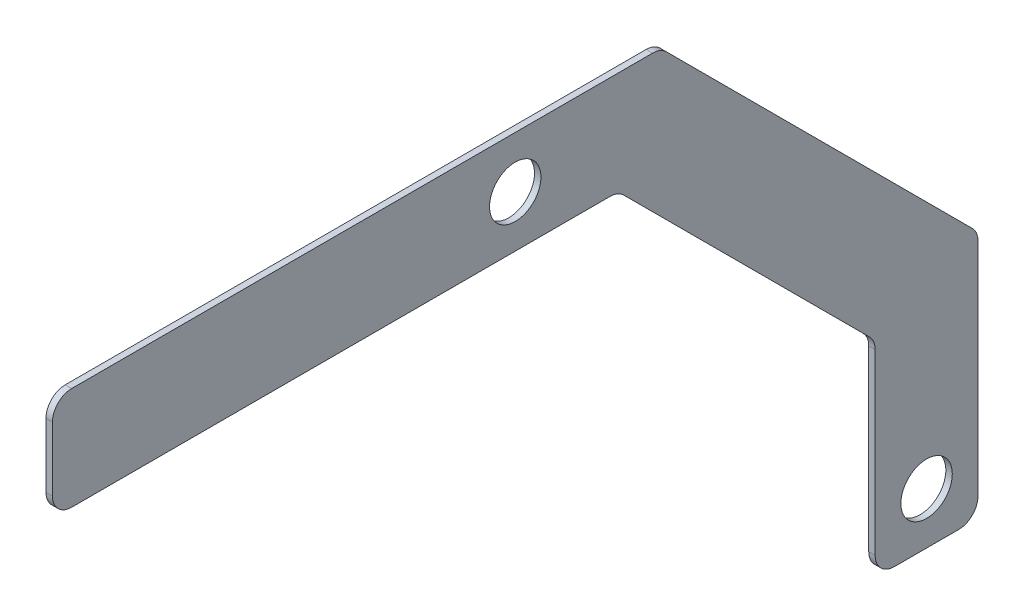
SolidWorks part; units mm, degrees
material "6063-O"
ref_plane "Front" through (0, 0, 0) normal (0, 0, 1) x (1, 0, 0)
ref_plane "Top" through (0, 0, 0) normal (0, 1, 0) x (1, 0, 0)
ref_plane "Right" through (0, 0, 0) normal (1, 0, 0) x (0, 0, -1)
sketch "Sketch1" plane through (0, 0, 0) normal (1, 0, 0) x (0, 0, -1)
  line L0 (0, 25.4) -> (0, -25.4) construction
  line L1 (-228.6, 25.4) -> (228.6, 25.4)
  line L2 (-228.6, 25.4) -> (-228.6, -254)
  line L3 (-177.8, -25.4) -> (177.8, -25.4)
  line L4 (228.6, 25.4) -> (228.6, -254)
  line L7 (228.6, -254) -> (177.8, -254)
  line L8 (177.8, -25.4) -> (177.8, -254)
  line L11 (-228.6, -254) -> (-177.8, -254)
  line L12 (-177.8, -25.4) -> (-177.8, -254)
  circle A0 centre (0, 0) radius 12.7
  point P12 (0, 0)
  dimension "D5" = 25.4
  dimension "D1" = 50.8
  dimension "D2" = 50.8
  dimension "D3" = 457.2
  dimension "D4" = 228.6
extrude "Boss-Extrude1" add sketch "Sketch1" along normal blind 3.175
sketch "Sketch3" plane through (3.175, 0, 0) normal (1, 0, 0) x (0, 0, -1)
  line L0 (-279.2989, -228.6) -> (49720.7011, -228.6) construction
  line L1 (-228.6, -254) -> (-177.8, -254) construction
  line L2 (-203.2, -254) -> (-203.2, 25.4) construction
  line L3 (228.6, 25.4) -> (-228.6, 25.4) construction
  line L4 (203.2, -254) -> (203.2, 25.4) construction
  line L5 (177.8, -254) -> (228.6, -254) construction
  circle A0 centre (-203.2, -228.6) radius 12.7
  circle A1 centre (203.2, -228.6) radius 12.7
  point P12 (-203.2, -228.6)
  point P13 (203.2, -228.6)
  dimension "D2" = 25.4
  dimension "D1" = 25.4
extrude "Cut-Extrude1" cut sketch "Sketch3" against normal through all
sketch "Sketch4" plane through (3.175, 0, 0) normal (1, 0, 0) x (0, 0, -1)
  line L1 (-177.8, -25.4) -> (-228.6, -25.4)
  line L2 (-177.8, -25.4) -> (-177.8, -254)
  line L3 (-177.8, -254) -> (-228.6, -254)
  line L4 (-228.6, -25.4) -> (-228.6, -254)
extrude "Cut-Extrude2" cut sketch "Sketch4" against normal through all
sketch "Sketch5" plane through (3.175, 0, 0) normal (1, 0, 0) x (0, 0, -1)
  line L0 (50.8, -25.4) -> (177.8, -152.4)
  line L1 (-228.6, -25.4) -> (177.8, -25.4) construction
  line L2 (177.8, -25.4) -> (177.8, -254) construction
  line L3 (50.8, -25.4) -> (177.8, -25.4)
  line L4 (177.8, -25.4) -> (177.8, -152.4)
  dimension "D1" = 45
  dimension "D2" = 127
extrude "Boss-Extrude2" add sketch "Sketch5" against normal blind 3.175
sketch "Sketch6" plane through (3.175, 0, 0) normal (1, 0, 0) x (0, 0, -1)
  line L0 (71.842, 25.4) -> (228.6, -131.358)
  line L1 (228.6, 25.4) -> (-228.6, 25.4) construction
  line L2 (228.6, -254) -> (228.6, 25.4) construction
  line L3 (228.6, -131.358) -> (228.6, 25.4)
  line L4 (228.6, 25.4) -> (71.842, 25.4)
  line L9 (50.8, -25.4) -> (177.8, -152.4) construction
  dimension "D1" = 50.8
extrude "Cut-Extrude3" cut sketch "Sketch6" against normal through all
fillet "Fillet1" radius 9.525 8 edges at (1.5875, -254, -228.6) (1.5875, -254, -177.8) (1.5875, -152.4, -177.8) (1.5875, -131.358, -228.6) (1.5875, 25.4, -71.842) (1.5875, -25.4, -50.8) (1.5875, -25.4, 228.6) (1.5875, 25.4, 228.6)
